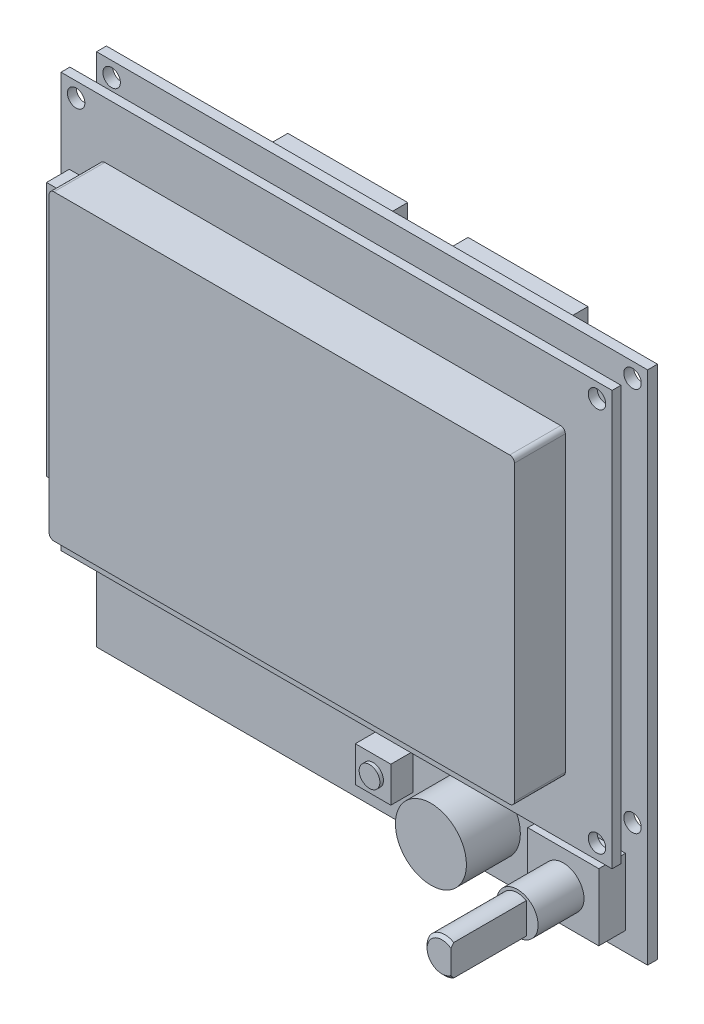
SolidWorks part; units mm, degrees
ref_plane "Front Plane" through (0, 0, 0) normal (0, 0, 1) x (1, 0, 0)
ref_plane "Top Plane" through (0, 0, 0) normal (0, 1, 0) x (1, 0, 0)
ref_plane "Right Plane" through (0, 0, 0) normal (1, 0, 0) x (0, 0, -1)
sketch "Sketch1" plane through (0, 0, 0) normal (0, 0, 1) x (1, 0, 0)
  line L0 (2.55, -2.5) -> (90.55, -2.5) construction
  line L1 (0, 0) -> (93.1, 0)
  line L2 (0, 0) -> (0, -87.1)
  line L3 (0, -87.1) -> (93.1, -87.1)
  line L4 (93.1, 0) -> (93.1, -87.1)
  line L5 (46.55, -2.5) -> (46.55, 0) construction
  circle A0 centre (2.55, -2.5) radius 1.475
  circle A1 centre (90.55, -2.5) radius 1.475
  circle A2 centre (2.55, -67.5) radius 1.475
  circle A3 centre (90.55, -67.5) radius 1.475
  dimension "D6" = 2.95
  dimension "D1" = 87.1
  dimension "D2" = 93.1
  dimension "D3" = 88
  dimension "D4" = 65
  dimension "D5" = 2.5
extrude "Boss-Extrude1" add sketch "Sketch1" along normal blind 1.67
sketch "Sketch2" plane through (0, 0, 1.67) normal (0, 0, 1) x (1, 0, 0)
  line L0 (93.1, -87.1) -> (93.1, 0) construction
  line L1 (0, 0) -> (93.1, 0)
  line L2 (0, 0) -> (0, -70)
  line L3 (0, -70) -> (93.1, -70)
  line L4 (93.1, 0) -> (93.1, -70)
  circle A0 centre (2.55, -2.5) radius 1.475 construction
  circle A1 centre (2.55, -67.5) radius 1.475 construction
  circle A2 centre (90.55, -67.5) radius 1.475 construction
  circle A3 centre (90.55, -2.5) radius 1.475 construction
  circle A4 centre (2.55, -2.5) radius 1.475
  circle A5 centre (2.55, -67.5) radius 1.475
  circle A6 centre (90.55, -67.5) radius 1.475
  circle A7 centre (90.55, -2.5) radius 1.475
  dimension "D1" = 70
extrude "Boss-Extrude2" add sketch "Sketch2" along normal blind 1.5 from offset 4.5 separate body
sketch "Sketch3" plane through (0, 0, 7.67) normal (0, 0, 1) x (1, 0, 0)
  line L0 (93.1, 0) -> (0, 0) construction
  line L1 (7.4, -9.5) -> (84.4, -9.5)
  line L2 (6.6, -10.3) -> (6.6, -59.8)
  line L3 (7.4, -60.6) -> (84.4, -60.6)
  line L4 (85.2, -10.3) -> (85.2, -59.8)
  line L5 (0, 0) -> (0, -70) construction
  arc A0 (84.4, -9.5) -> (85.2, -10.3) centre (84.4, -10.3) cw
  arc A1 (84.4, -60.6) -> (85.2, -59.8) centre (84.4, -59.8) ccw
  arc A2 (6.6, -59.8) -> (7.4, -60.6) centre (7.4, -59.8) ccw
  arc A3 (7.4, -9.5) -> (6.6, -10.3) centre (7.4, -10.3) ccw
  point P10 (85.2, -9.5)
  point P15 (6.6, -60.6)
  point P18 (6.6, -9.5)
  dimension "D5" = 0.8
  dimension "D1" = 60.6
  dimension "D2" = 51.1
  dimension "D3" = 85.2
  dimension "D4" = 78.6
extrude "Boss-Extrude3" add sketch "Sketch3" along normal blind 8.6
sketch "Sketch4" plane through (0, 0, 7.67) normal (0, 0, 1) x (1, 0, 0)
  line L0 (6.6, -10.3) -> (6.6, -59.8) construction
  line L1 (6.6, -13.5) -> (1.4, -13.5)
  line L2 (6.6, -13.5) -> (6.6, -56.5)
  line L3 (6.6, -56.5) -> (1.4, -56.5)
  line L4 (1.4, -13.5) -> (1.4, -56.5)
  line L5 (93.1, 0) -> (0, 0) construction
  line L6 (85.2, -59.8) -> (85.2, -10.3) construction
  dimension "D1" = 56.5
  dimension "D2" = 43
  dimension "D3" = 83.8
extrude "Boss-Extrude4" add sketch "Sketch4" along normal blind 3.85
sketch "Sketch5" plane through (0, 0, 1.67) normal (0, 0, 1) x (1, 0, 0)
  line L0 (0, -87.1) -> (93.1, -87.1) construction
  line L1 (47.5, -75.6) -> (53.5, -75.6)
  line L2 (47.5, -75.6) -> (47.5, -81.6)
  line L3 (47.5, -81.6) -> (53.5, -81.6)
  line L4 (53.5, -75.6) -> (53.5, -81.6)
  line L5 (0, 0) -> (0, -87.1) construction
  dimension "D1" = 11.5
  dimension "D2" = 53.5
  dimension "D3" = 6
  dimension "D4" = 6
extrude "Boss-Extrude5" add sketch "Sketch5" along normal blind 3.78
sketch "Sketch6" plane through (0, 0, 5.45) normal (0, 0, 1) x (1, 0, 0)
  line L0 (47.5, -75.6) -> (53.5, -81.6) construction
  circle A0 centre (50.5, -78.6) radius 1.75
  dimension "D1" = 3.5
extrude "Boss-Extrude6" add sketch "Sketch6" along normal blind 0.6
sketch "Sketch7" plane through (0, 0, 1.67) normal (0, 0, 1) x (1, 0, 0)
  line L0 (93.1, -87.1) -> (93.1, 0) construction
  line L1 (0, -87.1) -> (93.1, -87.1) construction
  circle A0 centre (65.6, -78.6) radius 6
  dimension "D1" = 33.5
  dimension "D3" = 12
  dimension "D2" = 14.5
extrude "Boss-Extrude7" add sketch "Sketch7" along normal blind 9.11
sketch "Sketch8" plane through (0, 0, 1.67) normal (0, 0, 1) x (1, 0, 0)
  line L0 (0, -87.1) -> (93.1, -87.1) construction
  line L1 (77.35, -72.6) -> (89.35, -72.6)
  line L2 (77.35, -72.6) -> (77.35, -83.9)
  line L3 (77.35, -83.9) -> (89.35, -83.9)
  line L4 (89.35, -72.6) -> (89.35, -83.9)
  line L5 (93.1, -87.1) -> (93.1, 0) construction
  dimension "D1" = 14.5
  dimension "D2" = 11.3
  dimension "D3" = 15.75
  dimension "D4" = 12
extrude "Boss-Extrude8" add sketch "Sketch8" along normal blind 4.5
sketch "Sketch9" plane through (0, 0, 6.17) normal (0, 0, 1) x (1, 0, 0)
  line L0 (77.35, -72.6) -> (89.35, -83.9) construction
  line L1 (89.35, -72.6) -> (77.35, -72.6) construction
  line L2 (77.35, -72.6) -> (77.35, -83.9) construction
  line L3 (77.35, -83.9) -> (89.35, -83.9) construction
  circle A0 centre (83.35, -78.25) radius 3.5
  dimension "D1" = 7
extrude "Boss-Extrude10" add sketch "Sketch9" along normal offset from surface (7.75 mm away) 12.25 up to face at (71.6, -78.6, 1.67) offset beyond the face yes
sketch "Sketch11" plane through (0, 0, 13.92) normal (0, 0, 1) x (1, 0, 0)
  line L0 (84.85, -75.6519) -> (84.85, -80.8481)
  arc A0 (84.85, -75.6519) -> (84.85, -80.8481) centre (83.35, -78.25) ccw
  dimension "D1" = 3
  dimension "D2" = 4.5
extrude "Boss-Extrude11" add sketch "Sketch11" along normal offset from surface (12.75 mm away) 25 up to face at (71.6, -78.6, 1.67) offset beyond the face yes
chamfer "Chamfer1" distance 0.5 angle 45 1 edges at (80.35, -78.25, 26.67)
sketch "Sketch12" plane through (0, 0, 0) normal (0, 0, -1) x (-1, 0, 0)
  line L0 (-93.1, -87.1) -> (-93.1, 0) construction
  line L1 (-72.35, -6.45) -> (-52.1, -6.45)
  line L2 (-72.35, -6.45) -> (-72.35, -15.4)
  line L3 (-72.35, -15.4) -> (-52.1, -15.4)
  line L4 (-52.1, -6.45) -> (-52.1, -15.4)
  line L5 (-41.9, -6.45) -> (-21.65, -6.45)
  line L6 (-41.9, -6.45) -> (-41.9, -15.4)
  line L7 (-41.9, -15.4) -> (-21.65, -15.4)
  line L8 (-21.65, -6.45) -> (-21.65, -15.4)
  line L9 (-93.1, 0) -> (0, 0) construction
  dimension "D1" = 20.25
  dimension "D2" = 8.95
  dimension "D3" = 41
  dimension "D4" = 50.7
  dimension "D5" = 15.4
extrude "Boss-Extrude12" add sketch "Sketch12" along normal blind 9
sketch "Sketch13" plane through (0, 0, 0) normal (0, 0, -1) x (-1, 0, 0)
  line L0 (0, 0) -> (0, -87.1) construction
  line L1 (0, -22.2) -> (-26, -22.2)
  line L2 (0, -22.2) -> (0, -48.6)
  line L3 (0, -48.6) -> (-26, -48.6)
  line L4 (-26, -22.2) -> (-26, -48.6)
  line L5 (-93.1, 0) -> (0, 0) construction
  dimension "D1" = 26
  dimension "D2" = 26.4
  dimension "D3" = 48.6
extrude "Boss-Extrude13" add sketch "Sketch13" along normal blind 3.5
